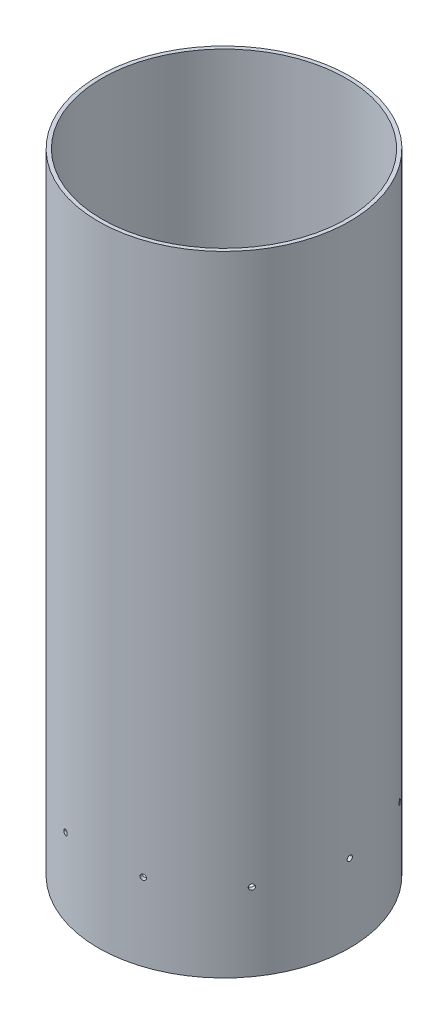
SolidWorks part; units mm, degrees
material "S-Glass Fiber"
ref_plane "Front Plane" through (0, 0, 0) normal (0, 0, 1) x (1, 0, 0)
ref_plane "Top Plane" through (0, 0, 0) normal (0, 1, 0) x (1, 0, 0)
ref_plane "Right Plane" through (0, 0, 0) normal (1, 0, 0) x (0, 0, -1)
sketch "Sketch2" plane through (0, 0, 0) normal (0, 1, 0) x (1, 0, 0)
  circle A0 centre (0, 0) radius 76.1746
  circle A1 centre (0, 0) radius 73.914
  dimension "D1" = 152.3492
  dimension "D2" = 147.828
extrude "Boss-Extrude1" add sketch "Sketch2" along normal blind 381
ref_plane "Plane1" through (76.1746, 0, 0) normal (1, 0, 0) x (0, 0, -1)
sketch "Sketch3" plane through (76.1746, 0, 0) normal (1, 0, 0) x (0, 0, -1)
  line L0 (0, 0) -> (0, 46.99) construction
  dimension "D1" = 46.99
hole_wizard "1/8 (0.1250) Dowel Hole1" positions "Sketch4" profile "Sketch5" hole size "1/8" standard "ANSI Inch"
sketch "Sketch4" plane through (76.1746, 0, 0) normal (1, 0, 0) x (0, 0, -1)
  point P0 (0, 46.99)
sketch "Sketch5" plane through (76.1746, 46.99, 0) normal (0, 1, 0) x (0, 0, -1)
  line L0 (0, 0) -> (0, 2.2606)
  line L1 (0, 2.2606) -> (1.5875, 2.2606)
  line L2 (1.5875, 2.2606) -> (1.5875, 0)
  line L5 (1.5875, 0) -> (0, 0)
  line L11 (0, -6.35) -> (0, 107.95) construction
  dimension "Thru Hole Dia." = 3.175
  dimension "Thru Hole Depth" = 2.2606
pattern_circular "CirPattern1" count 10 over 360 about axis through (0, 381, 0) along (0, -1, 0) of "1/8 (0.1250) Dowel Hole1"
